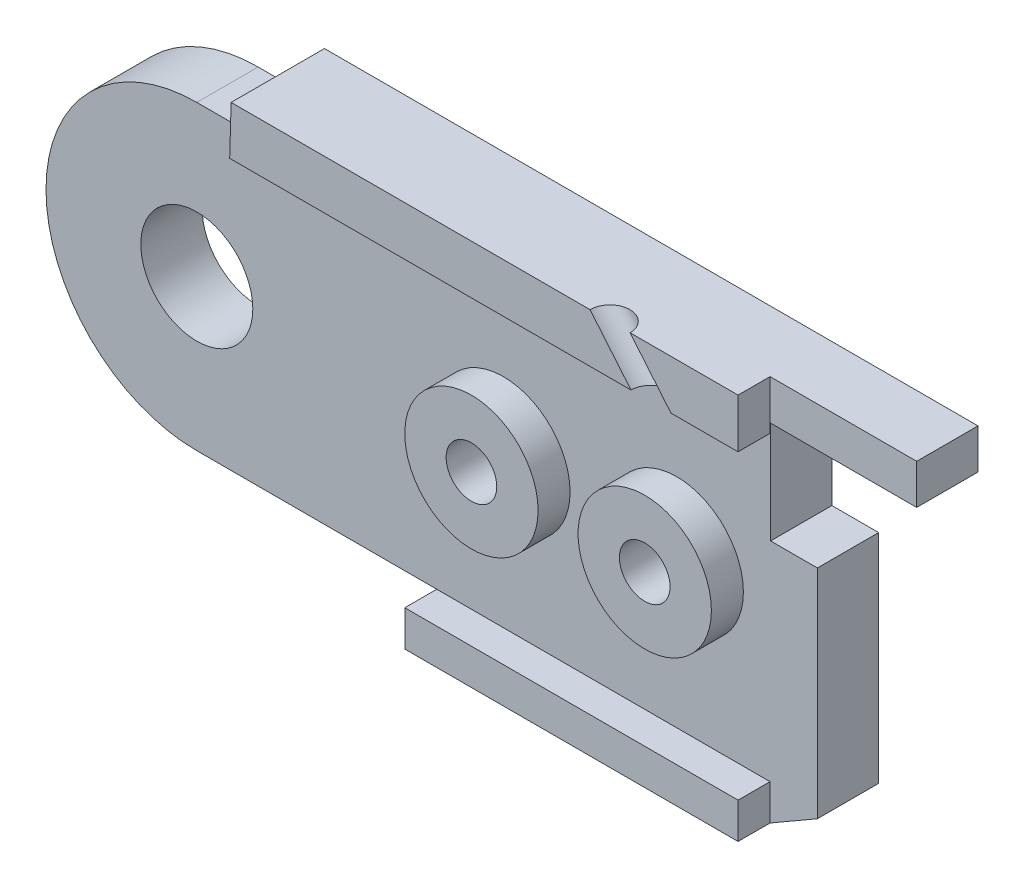
SolidWorks part; units mm, degrees
ref_plane "Front Plane" through (0, 0, 0) normal (0, 0, 1) x (1, 0, 0)
ref_plane "Top Plane" through (0, 0, 0) normal (0, 1, 0) x (1, 0, 0)
ref_plane "Right Plane" through (0, 0, 0) normal (1, 0, 0) x (0, 0, -1)
sketch "Sketch3" plane through (0, 0, 0) normal (0, 0, 1) x (1, 0, 0)
  line L7 (8, 0) -> (9, -2.5)
  line L11 (30, 7) -> (27, 7.5)
  line L13 (0, 7) -> (0, 7.5) construction
  line L14 (0, 7.5) -> (-22.3287, 7.5) construction
  line L15 (0, 5.3) -> (-14, 5.3) construction
  line L16 (0, 4) -> (-14, 4) construction
  line L17 (-14, 4) -> (-14, 5.3) construction
  line L18 (5.6569, 5.6569) -> (5.6569, 7.5)
  line L19 (5.6569, 7.5) -> (27, 7.5)
  line L20 (21.5, -7) -> (9, -7)
  line L21 (9, -7) -> (9, -2.5)
  line L23 (25.0503, -4.9497) -> (21.5, -7)
  arc A4 (8, 0) -> (5.6569, 5.6569) centre (0, 0) ccw
  arc A5 (25.0503, -4.9497) -> (30, 7) centre (30, 0) ccw
  circle A6 centre (0, 0) radius 7 construction
  circle A7 centre (0, 0) radius 3.9 construction
  circle A8 centre (0, 0) radius 5.3 construction
  circle A9 centre (0, 0) radius 4 construction
  dimension "D10" = 0.5
  dimension "D17" = 14
  dimension "D5" = 135
  dimension "D6" = 12.5
  dimension "D7" = 4.5
  dimension "D8" = 1
  dimension "D9" = 45
  dimension "D11" = 1.8431
  dimension "D12" = 30
  dimension "D14" = 3
extrude "Boss-Extrude1" add sketch "Sketch3" along normal blind 2 contours A5 L11 L19 L18 A4 L7 L21 L20 L23
sketch "Sketch20" plane through (0, 0, 0) normal (0, 0, 1) x (1, 0, 0)
  line L0 (0, 7) -> (0, 7.5) construction
  line L1 (0, 7.5) -> (-19.4737, 7.5) construction
  line L2 (0, 5.3) -> (-14, 5.3) construction
  line L3 (0, 4) -> (-14, 4) construction
  line L4 (-14, 4) -> (-14, 5.3) construction
  line L5 (0, 5.3) -> (17.4849, 5.3) construction
  line L6 (17.4849, 5.3) -> (17.4849, 4) construction
  line L7 (17.4849, 4) -> (0, 4) construction
  line L8 (-2.5, 7.5) -> (-2.5, 2.868) construction
  circle A0 centre (0, 0) radius 7 construction
  circle A1 centre (0, 0) radius 3.9 construction
  circle A3 centre (0, 0) radius 5.3 construction
  circle A4 centre (0, 0) radius 4 construction
  circle A5 centre (0, 0) radius 2 construction
  dimension "D1" = 0
  dimension "D2" = 2.5
ref_plane "Plane1" through (0, 0, 2) normal (0, 0, 1) x (1, 0, 0)
sketch "Sketch4" plane through (0, 0, 2) normal (0, 0, 1) x (1, 0, 0)
  line L4 (5.6569, 5.6569) -> (5.6569, 7.5)
  line L5 (5.6569, 5.6569) -> (5.6569, 7.5) construction
  line L6 (5.6569, 7.5) -> (21.5, 7.5)
  line L10 (8, 0) -> (9, -2.5)
  line L11 (9, -2.5) -> (9, -7)
  line L12 (9, -7) -> (21.5, -7)
  line L13 (21.5, -7) -> (21.5, 7.5)
  arc A0 (8, 0) -> (5.6569, 5.6569) centre (0, 0) ccw construction
  arc A3 (8, 0) -> (5.6569, 5.6569) centre (0, 0) ccw
sketch "Sketch22" plane through (0, 0, 2) normal (0, 0, 1) x (1, 0, 0)
  line L0 (5.6569, 5.6569) -> (2.4868, 5.6569)
  line L1 (5.6569, 7.5) -> (21.5, 7.5)
  line L2 (5.6569, 7.5) -> (2.4868, 7.5)
  line L3 (2.4868, 7.5) -> (2.4868, 5.6569)
  line L6 (8, 0) -> (9, -2.5)
  line L7 (9, -2.5) -> (9, -7)
  line L8 (9, -7) -> (21.5, -7)
  line L10 (21.5, 7.5) -> (27, 7.5)
  line L11 (27, 7.5) -> (27, 2.172)
  line L12 (27, 2.172) -> (23.2751, 2.172)
  line L13 (21.5, -7) -> (23.2751, -5.9749)
  line L14 (25.0503, -4.9497) -> (21.5, -7) construction
  line L15 (23.2751, -5.9749) -> (23.2751, 2.172)
  arc A0 (8, 0) -> (5.6569, 5.6569) centre (0, 0) ccw
extrude "Boss-Extrude6" add sketch "Sketch22" along normal blind 2.5
sketch "Sketch25" plane through (0, 0, 2) normal (0, 0, 1) x (1, 0, 0)
  line L0 (0, 5.3) -> (18.0981, 5.3) construction
  line L1 (0, 4) -> (18.0981, 4) construction
  line L2 (18.0981, 4) -> (18.0981, 5.3) construction
sketch "Sketch26" plane through (0, 0, 2) normal (0, 0, 1) x (1, 0, 0)
  line L1 (18.0981, 5.3) -> (2.5301, 5.3)
  line L2 (18.0981, 4) -> (2.5301, 4)
  line L3 (2.5301, 5.3) -> (2.5301, 4)
  line L4 (18.0981, 5.3) -> (27, 5.3)
  line L5 (27, 2.172) -> (27, 7.5) construction
  line L6 (27, 5.3) -> (27, 4)
  line L7 (27, 4) -> (18.0981, 4)
extrude "Cut-Extrude6" cut sketch "Sketch26" along normal blind 2.5
ref_plane "Plane18" through (0, 0, 4.5) normal (0, 0, 1) x (1, 0, 0)
sketch "Sketch31" plane through (0, 0, 4.5) normal (0, 0, 1) x (1, 0, 0)
  line L0 (2.4327, 5.6569) -> (0, 5.6569)
  line L4 (9, -5.6569) -> (0, -5.6569)
  line L5 (2.4327, 5.6569) -> (2.4868, 7.5)
  line L12 (9, -7) -> (9, -5.6569)
  line L13 (9, -2.5) -> (9, -7) construction
  line L16 (27, 7.5) -> (27, 2.172)
  line L17 (27, 2.172) -> (23.2751, 2.172)
  line L18 (23.2751, -5.9749) -> (23.2751, 2.172)
  line L19 (27, 7.5) -> (2.4868, 7.5)
  line L20 (9, -7) -> (21.5, -7)
  line L21 (21.5, -7) -> (23.2751, -5.9749)
  arc A0 (0, 5.6569) -> (0, -5.6569) centre (0, 0) ccw
  dimension "D1" = 5.6569
extrude "Boss-Extrude14" add sketch "Sketch31" along normal blind 2.3 separate body
sketch "Sketch32" plane through (0, 0, 6.8) normal (0, 0, 1) x (1, 0, 0)
  circle A0 centre (0, 0) radius 2.1
extrude "Cut-Extrude7" cut sketch "Sketch32" against normal blind 2.3
sketch "Sketch33" plane through (0, 0, 6.8) normal (0, 0, 1) x (1, 0, 0)
  line L4 (9, -5.6569) -> (9, -7)
  line L11 (9, -7) -> (21.5, -7)
  line L15 (21.5, -7) -> (21.5, -5.6569)
  line L16 (21.5, -5.6569) -> (9, -5.6569)
  line L17 (2.4868, 7.5) -> (21.5, 7.5)
  line L18 (27, 7.5) -> (2.4868, 7.5) construction
  line L19 (2.4868, 7.5) -> (2.4327, 5.6569)
  line L20 (2.4327, 5.6569) -> (21.5, 5.6569)
  line L21 (21.5, 5.6569) -> (21.5, 7.5)
extrude "Boss-Extrude15" add sketch "Sketch33" along normal blind 1.2
sketch "Sketch34" plane through (0, 0, 2) normal (0, 0, 1) x (1, 0, 0)
  line L0 (30, 5.3) -> (18.0981, 5.3) construction
  line L1 (30, 4) -> (18.0981, 4) construction
  circle A0 centre (30, 0) radius 2 construction
  circle A1 centre (30, 0) radius 5.3 construction
  circle A2 centre (30, 0) radius 4 construction
sketch "Sketch35" plane through (0, 0, 6.8) normal (0, 0, 1) x (1, 0, 0)
  line L0 (27, 2.172) -> (27, 6)
  line L1 (27, 2.172) -> (21.5204, 2.172)
  line L2 (27, 6) -> (21.5204, 6)
  line L3 (21.5204, 2.172) -> (21.5204, 6)
  line L4 (27, 2.172) -> (27, 7.5) construction
extrude "Cut-Extrude8" cut sketch "Sketch35" against normal blind 2.4
sketch "Sketch36" plane through (0, 0, 4.4) normal (0, 0, 1) x (1, 0, 0)
  line L0 (27, 2.172) -> (27, 4)
  line L1 (27, 2.172) -> (23.3, 2.172)
  line L2 (27, 4) -> (23.3, 4)
  line L3 (23.3, 2.172) -> (23.3, 4)
  line L4 (21.5, -7) -> (21.5, 7.5) construction
  dimension "D1" = 1.8
extrude "Cut-Extrude9" cut sketch "Sketch36" against normal blind 2.4
sketch "Sketch37" plane through (0, 0, 2) normal (0, 0, 1) x (1, 0, 0)
  circle A0 centre (30, 0) radius 3.9
extrude "Boss-Extrude16" add sketch "Sketch37" along normal blind 2.3
sketch "Sketch39" plane through (0, 0, 4.3) normal (0, 0, 1) x (1, 0, 0)
  line L0 (29, 1.7321) -> (29, -1.7321)
  arc A0 (29, -1.7321) -> (29, 1.7321) centre (30, 0) ccw
  dimension "D2" = 4
  dimension "D1" = 1
extrude "Cut-Extrude10" cut sketch "Sketch39" against normal through all
sketch "Sketch43" plane through (0, 0, 6.8) normal (0, 0, 1) x (1, 0, 0)
  line L2 (0, -5.6569) -> (9, -5.6569) construction
  circle A0 centre (11.5, 0) radius 2.5
  circle A1 centre (18, 0) radius 2.5
  dimension "D1" = 2.5
  dimension "D3" = 5
  dimension "D4" = 6.5
  dimension "D2" = 5.6569
extrude "Boss-Extrude17" add sketch "Sketch43" along normal blind 1.2
sketch "Sketch44" plane through (0, 0, 8) normal (0, 0, 1) x (1, 0, 0)
  circle A0 centre (11.5, 0) radius 0.95
  circle A1 centre (18, 0) radius 0.95
  dimension "D1" = 1.9
  dimension "D2" = 1.9
extrude "Cut-Extrude11" cut sketch "Sketch44" against normal through all
sketch "Sketch45" plane through (0, 0, 0) normal (0, 0, -1) x (-1, 0, 0)
  circle A0 centre (-11.5, 0) radius 2
  circle A1 centre (-18, 0) radius 2
extrude "Cut-Extrude12" cut sketch "Sketch45" against normal blind 2.5
ref_plane "Plane17" through (0, 0, 8) normal (0, 0, 1) x (1, 0, 0)
sketch "Sketch48" plane through (0, 0, 2) normal (0, 0, 1) x (1, 0, 0)
  circle A0 centre (30, 0) radius 5 construction
sketch "Sketch51" plane through (0, 0, 8) normal (0, 0, 1) x (1, 0, 0)
  line L0 (18.2355, 5.6569) -> (27.0112, -4.8677) construction
  line L1 (2.4327, 5.6569) -> (21.5, 5.6569) construction
sketch "Sketch52" plane through (0, 5.6569, 0) normal (0, -1, 0) x (1, 0, 0)
  circle A0 centre (18.2355, 8) radius 0.75
extrude "Cut-Extrude13" cut sketch "Sketch52" along direction (0.6404, -0.768, 0) on the side against the normal blind 10
split "Split1" trim tools "Plane18" bodies to split 129 133 resulting bodies 134 135
delete or keep bodies "Body-Delete/Keep 1" type delete bodies bodies 134
